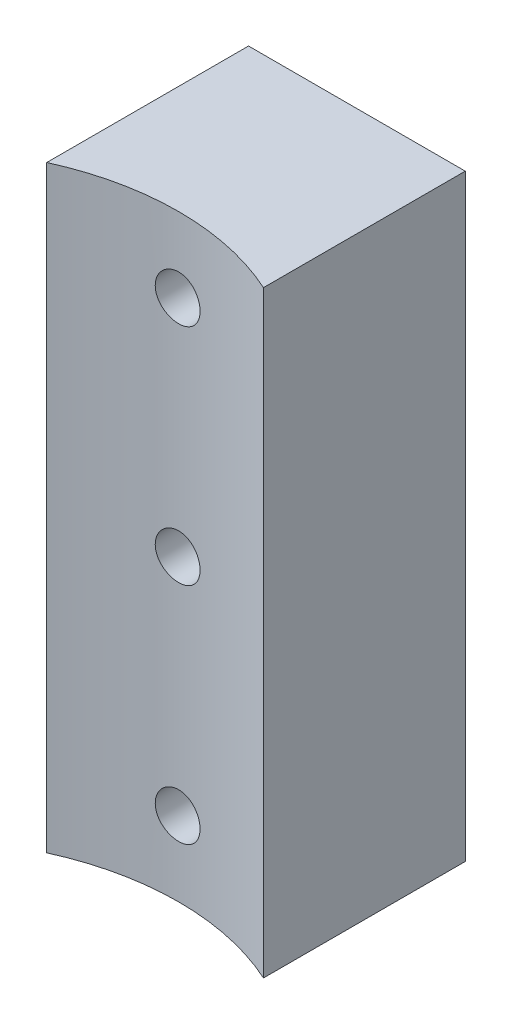
SolidWorks part; units mm, degrees
material "Mahogany"
ref_plane "Front Plane" through (0, 0, 0) normal (0, 0, 1) x (1, 0, 0)
ref_plane "Top Plane" through (0, 0, 0) normal (0, 1, 0) x (1, 0, 0)
ref_plane "Right Plane" through (0, 0, 0) normal (1, 0, 0) x (0, 0, -1)
sketch "Sketch1" plane through (0, 0, 0) normal (0, 1, 0) x (1, 0, 0)
  line L1 (-14.5, 13.5) -> (14.5, 13.5)
  line L2 (-14.5, 13.5) -> (-14.5, -13.5)
  line L4 (14.5, 13.5) -> (14.5, -13.5)
  line L5 (-14.5, 13.5) -> (14.5, -13.5) construction
  line L6 (-14.5, -13.5) -> (14.5, 13.5) construction
  arc A0 (-14.5, -13.5) -> (14.5, -13.5) centre (0, -45.3551) cw
  point P0 (0, 0)
  dimension "D3" = 35
  dimension "D1" = 29
  dimension "D2" = 27
extrude "Boss-Extrude1" add sketch "Sketch1" along normal blind 80
sketch "Sketch2" plane through (0, 0, -13.5) normal (0, 0, -1) x (-1, 0, 0)
  line L0 (-14.5, 0) -> (14.5, 0) construction
  line L1 (-14.5, 80) -> (-14.5, 0) construction
  circle A0 centre (0, 70) radius 3
  circle A1 centre (0, 40) radius 3
  circle A2 centre (0, 10) radius 3
  point P6 (0, 0)
  point P9 (0, 0)
  point P10 (0, 0)
  point P12 (72.2961, 84.2586)
  point P14 (-14.5, 40)
  dimension "D3" = 6
  dimension "D1" = 30
  dimension "D2" = 30
extrude "Cut-Extrude1" cut sketch "Sketch2" against normal through all
